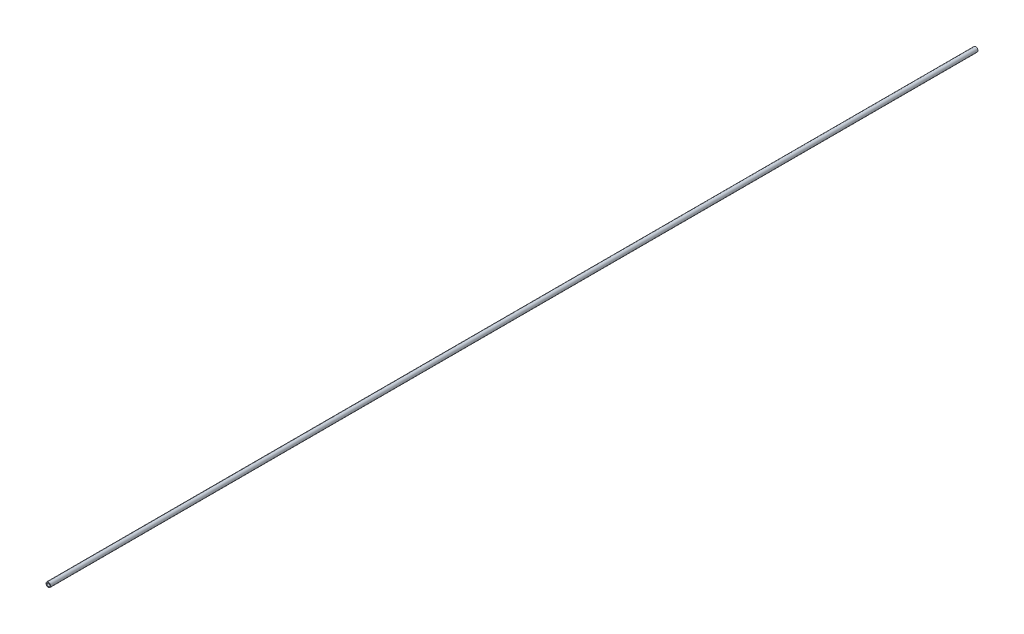
SolidWorks part; units mm, degrees
ref_plane "Front" through (0, 0, 0) normal (0, 0, 1) x (1, 0, 0)
ref_plane "Top" through (0, 0, 0) normal (0, 1, 0) x (1, 0, 0)
ref_plane "Right" through (0, 0, 0) normal (1, 0, 0) x (0, 0, -1)
sketch "Sketch1" plane through (0, 0, 0) normal (0, 0, 1) x (1, 0, 0)
  circle A0 centre (0, 0) radius 1.6
  circle A1 centre (0, 0) radius 2.5
extrude "Boss-Extrude1" add sketch "Sketch1" along normal blind 1000
